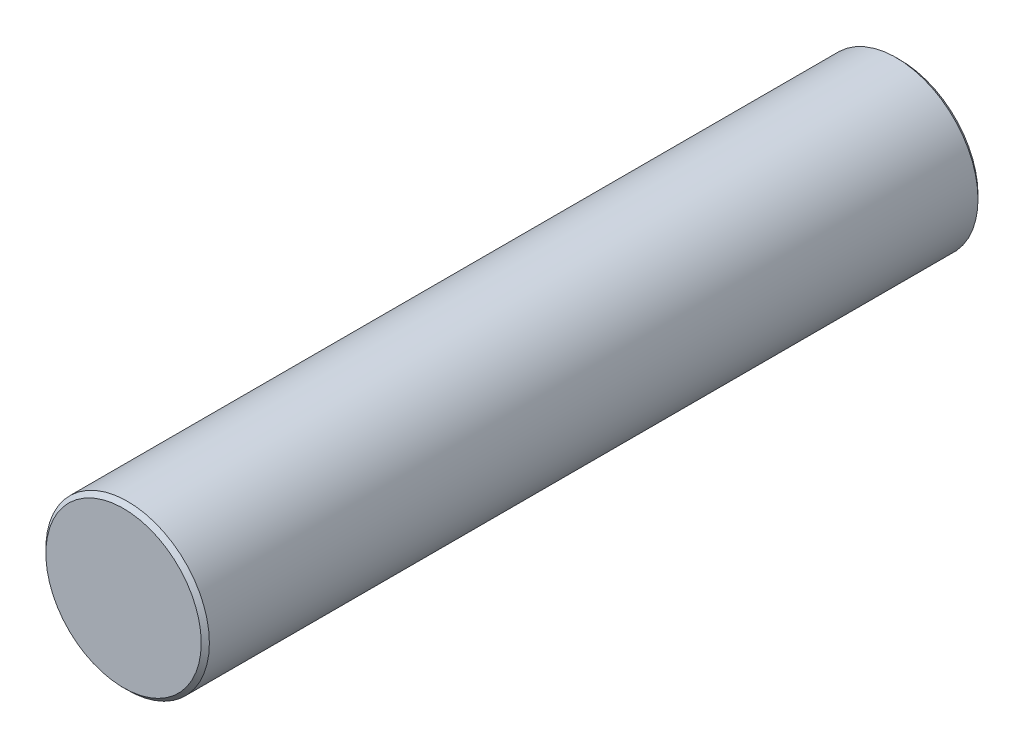
SolidWorks part; units mm, degrees
material "Cast Alloy Steel"
ref_plane "Front Plane" through (0, 0, 0) normal (0, 0, 1) x (1, 0, 0)
ref_plane "Top Plane" through (0, 0, 0) normal (0, 1, 0) x (1, 0, 0)
ref_plane "Right Plane" through (0, 0, 0) normal (1, 0, 0) x (0, 0, -1)
sketch "Sketch1" plane through (0, 0, 0) normal (0, 0, 1) x (1, 0, 0)
  circle A0 centre (0, 0) radius 20
  dimension "D1" = 40
extrude "Boss-Extrude1" add sketch "Sketch1" along normal blind 190
chamfer "Chamfer1" distance 1 angle 45 2 edges at (20, 0, 0) (20, 0, 190)
